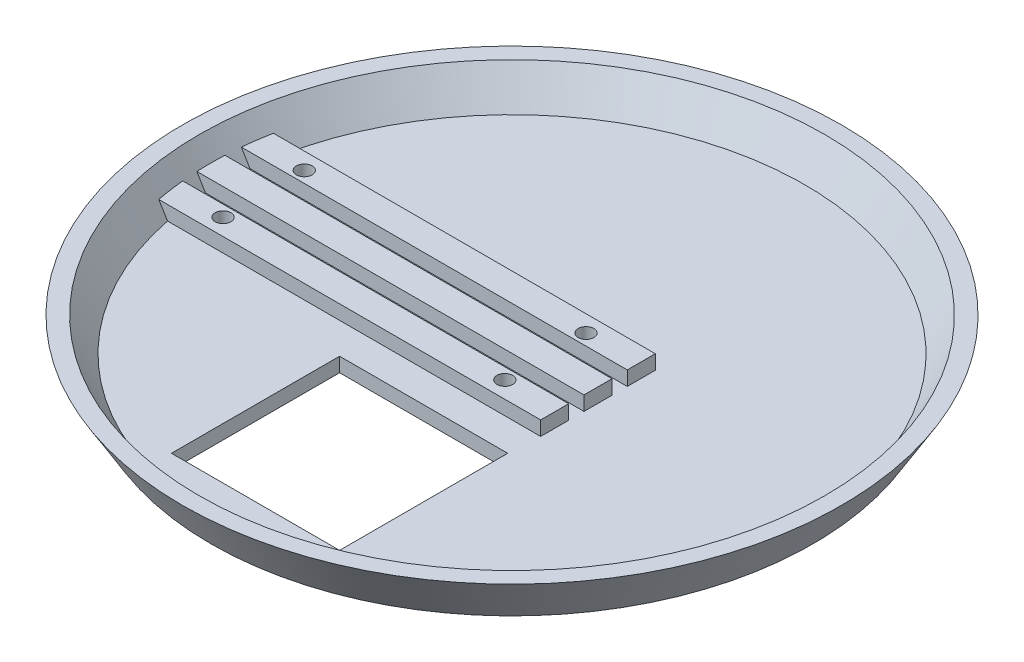
SolidWorks part; units mm, degrees
ref_plane "Front Plane" through (0, 0, 0) normal (0, 0, 1) x (1, 0, 0)
ref_plane "Top Plane" through (0, 0, 0) normal (0, 1, 0) x (1, 0, 0)
ref_plane "Right Plane" through (0, 0, 0) normal (1, 0, 0) x (0, 0, -1)
sketch "Sketch1" plane through (0, 0, 0) normal (0, 0, 1) x (1, 0, 0)
  line L0 (0, 0) -> (63, 0)
  line L1 (63, 0) -> (69, 10)
  line L6 (0, 3) -> (61.3014, 3)
  line L7 (61.3014, 3) -> (65.5014, 10)
  line L8 (69, 10) -> (65.5014, 10)
  line L9 (0, 0) -> (0, 3)
  line L10 (61.3014, 3) -> (66.4275, 11.5435) construction
  dimension "D1" = 69
  dimension "D2" = 63
  dimension "D3" = 10
  dimension "D4" = 3
revolve "Revolve1" add sketch "Sketch1" angle 360 about L9
sketch "Sketch2" plane through (0, 3, 0) normal (0, 1, 0) x (1, 0, 0)
  line L0 (-17.6, -18.5) -> (-17.6, -53.7)
  line L1 (-17.6, -18.5) -> (17.6, -18.5)
  line L5 (17.6, -18.5) -> (17.6, -53.7)
  line L6 (-17.6, -53.7) -> (17.6, -53.7)
  point P1 (0, -18.5)
  dimension "D2" = 35.2
  dimension "D1" = 35.2
  dimension "D4" = 18.5
extrude "Cut-Extrude1" cut sketch "Sketch2" against normal through all
sketch "Sketch4" plane through (0, 0, 0) normal (1, 0, 0) x (0, 0, -1)
  line L0 (-6.1333, 3) -> (-12, 3)
  line L5 (-12, 3) -> (-12, 6)
  line L6 (-12, 6) -> (-6.1333, 6)
  line L7 (-6.1333, 6) -> (-6.1333, 3)
  line L8 (-2.9333, 3) -> (2.9333, 3)
  line L9 (2.9333, 3) -> (2.9333, 6)
  line L10 (2.9333, 6) -> (-2.9333, 6)
  line L11 (-2.9333, 6) -> (-2.9333, 3)
  line L12 (12, 3) -> (6.1333, 3)
  line L13 (6.1333, 3) -> (6.1333, 6)
  line L14 (6.1333, 6) -> (12, 6)
  line L15 (12, 6) -> (12, 3)
  point P13 (0, 3)
  dimension "D1" = 12
  dimension "D2" = 3
  dimension "D3" = 3
  dimension "D4" = 3.2
  dimension "D5" = 3.2
  dimension "D6" = 12
extrude "Boss-Extrude1" add sketch "Sketch4" along normal blind 10 and the other way blind 63.5
sketch "Sketch5" plane through (0, 0, 0) normal (0, 1, 0) x (1, 0, 0)
  line L0 (10, 2.9333) -> (10, -2.9333) construction
  circle A0 centre (7, -8.5) radius 1.65
  circle A1 centre (7, 0) radius 1.65
  circle A2 centre (7, 8.5) radius 1.65
  circle A6 centre (-52, 8.5) radius 1.65
  circle A8 centre (-52, -8.5) radius 1.65
  circle A9 centre (-22.5, 0) radius 1.65
  circle A10 centre (-52, 0) radius 1.65
  circle A11 centre (-22.5, 8.5) radius 1.65
  circle A12 centre (-22.5, -8.5) radius 1.65
  dimension "D2" = 3.3
  dimension "D3" = 8.5
  dimension "D6" = 3
  dimension "D7" = 59
  dimension "D4" = 8.5
  dimension "D5" = 3
extrude "Cut-Extrude2" cut sketch "Sketch5" along normal through all contours A2 | A0 | A8 | A6
sketch "Sketch7" [suppressed] plane through (10, 0, 0) normal (1, 0, 0) x (0, 0, -1)
  line L0 (-12, 37.9) -> (-6.1333, 37.9) construction
  line L1 (-12, 3) -> (-6.1333, 3)
  line L2 (-12, 3) -> (-12, 43)
  line L3 (-12, 43) -> (12, 43)
  line L4 (12, 3) -> (12, 43)
  line L5 (-2.9333, 37.9) -> (2.9333, 37.9) construction
  line L6 (-6.1333, 37.9) -> (-2.9333, 37.9)
  line L7 (-6.1333, 37.9) -> (-6.1333, 40.9)
  line L8 (-6.1333, 40.9) -> (-2.9333, 40.9)
  line L9 (-2.9333, 37.9) -> (-2.9333, 40.9)
  line L10 (12, 37.9) -> (6.1333, 37.9) construction
  line L11 (2.9333, 3) -> (2.9333, 6)
  line L12 (2.9333, 37.9) -> (6.1333, 37.9)
  line L13 (2.9333, 37.9) -> (2.9333, 40.9)
  line L14 (2.9333, 40.9) -> (6.1333, 40.9)
  line L15 (6.1333, 37.9) -> (6.1333, 40.9)
  line L20 (2.9333, 6) -> (6.1333, 6)
  line L21 (6.1333, 6) -> (6.1333, 3)
  line L22 (-6.1333, 3) -> (-6.1333, 6)
  line L23 (-6.1333, 6) -> (-2.9333, 6)
  line L24 (-2.9333, 6) -> (-2.9333, 3)
  line L25 (6.1333, 3) -> (12, 3)
  line L26 (-2.9333, 3) -> (2.9333, 3)
  circle A0 centre (0, 23.5) radius 8.5
  point P18 (0, 3)
  dimension "D6" = 17
  dimension "D7" = 20.5
  dimension "D1" = 24
  dimension "D2" = 40
  dimension "D3" = 3.2
  dimension "D4" = 3
  dimension "D5" = 37.9
sketch "Sketch8" plane through (10, 0, 0) normal (1, 0, 0) x (0, 0, -1)
  line L1 (-12, 6) -> (-6.1333, 6)
  line L2 (-12, 6) -> (-12, 3)
  line L3 (-12, 3) -> (-6.1333, 3)
  line L4 (-6.1333, 6) -> (-6.1333, 3)
  line L5 (-2.9333, 6) -> (2.9333, 6)
  line L6 (-2.9333, 6) -> (-2.9333, 3)
  line L7 (-2.9333, 3) -> (2.9333, 3)
  line L8 (2.9333, 6) -> (2.9333, 3)
  line L9 (6.1333, 6) -> (12, 6)
  line L10 (6.1333, 6) -> (6.1333, 3)
  line L11 (6.1333, 3) -> (12, 3)
  line L12 (12, 6) -> (12, 3)
extrude "Boss-Extrude3" add sketch "Sketch8" along normal blind 8
